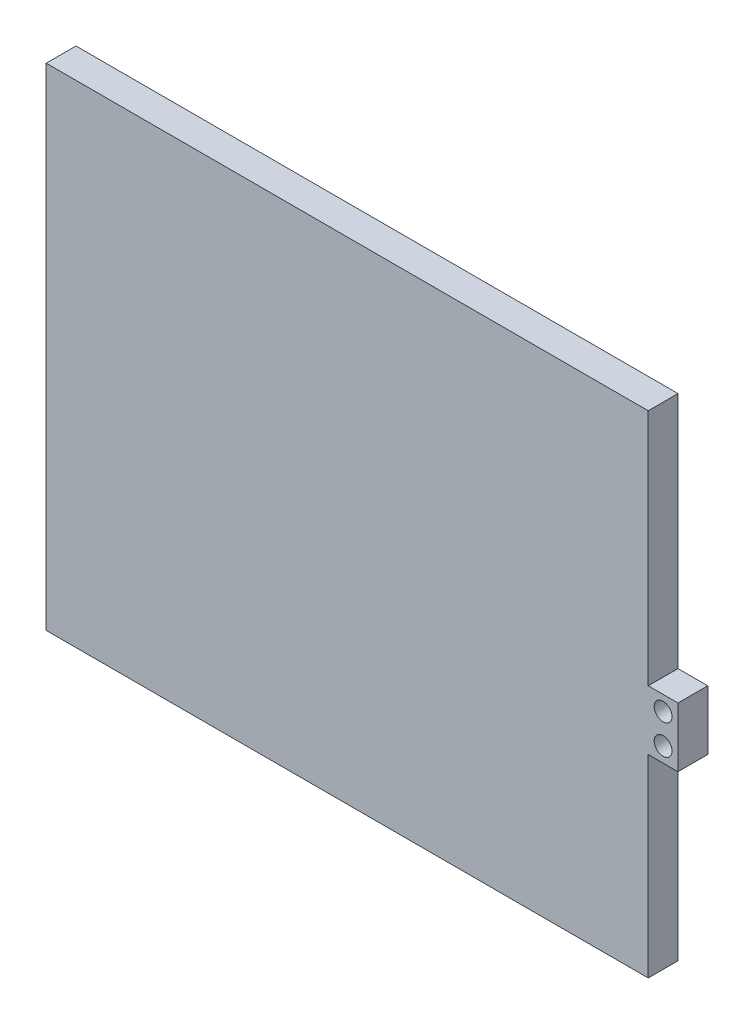
SolidWorks part; units mm, degrees
material "Polyurethane Foam Flexible"
ref_plane "Front Plane" through (0, 0, 0) normal (0, 0, 1) x (1, 0, 0)
ref_plane "Top Plane" through (0, 0, 0) normal (0, 1, 0) x (1, 0, 0)
ref_plane "Right Plane" through (0, 0, 0) normal (1, 0, 0) x (0, 0, -1)
sketch "Sketch2" plane through (0, 0, 0) normal (0, 0, 1) x (1, 0, 0)
  line L1 (-122.4216, 87.1773) -> (134.3724, 87.1773)
  line L2 (-122.4216, 87.1773) -> (-122.4216, -109.6727)
  line L3 (-122.4216, -109.6727) -> (134.3724, -109.6727)
  line L4 (134.3724, 87.1773) -> (134.3724, -109.6727)
  dimension "D1" = 196.85
  dimension "D2" = 256.794
extrude "Boss-Extrude1" add sketch "Sketch2" along normal blind 12.7
sketch "Sketch3" plane through (134.3724, 0, 0) normal (1, 0, 0) x (0, 0, -1)
  line L0 (-12.7, -109.6727) -> (-12.7, 87.1773) construction
  line L1 (-12.7, -1.7227) -> (0, -1.7227)
  line L2 (-12.7, -1.7227) -> (-12.7, -27.1227)
  line L3 (-12.7, -27.1227) -> (0, -27.1227)
  line L4 (0, -1.7227) -> (0, -27.1227)
  line L5 (0, -109.6727) -> (0, 87.1773) construction
  point P8 (0, -14.4227)
  dimension "D1" = 25.4
  dimension "D2" = 101.6
extrude "Boss-Extrude2" add sketch "Sketch3" along normal blind 12.7
sketch "Sketch4" plane through (0, 0, 0) normal (0, 0, -1) x (-1, 0, 0)
  line L7 (-147.0724, -27.1227) -> (-147.0724, -1.7227) construction
  line L8 (-147.0724, -1.7227) -> (-134.3724, -1.7227) construction
  circle A1 centre (-140.7224, -8.0727) radius 3.81
  circle A3 centre (-140.7224, -20.7727) radius 3.81
  dimension "D4" = 6.35
  dimension "D5" = 6.35
  dimension "D6" = 2
extrude "Cut-Extrude1" cut sketch "Sketch4" against normal blind 12.7
sketch "Sketch5" plane through (0, 87.1773, 0) normal (0, 1, 0) x (1, 0, 0)
  line L1 (-122.4216, 0) -> (134.3724, 0)
  line L2 (-122.4216, 0) -> (-122.4216, -12.7)
  line L3 (-122.4216, -12.7) -> (134.3724, -12.7)
  line L4 (134.3724, 0) -> (134.3724, -12.7)
extrude "Boss-Extrude3" add sketch "Sketch5" along normal blind 12.7
